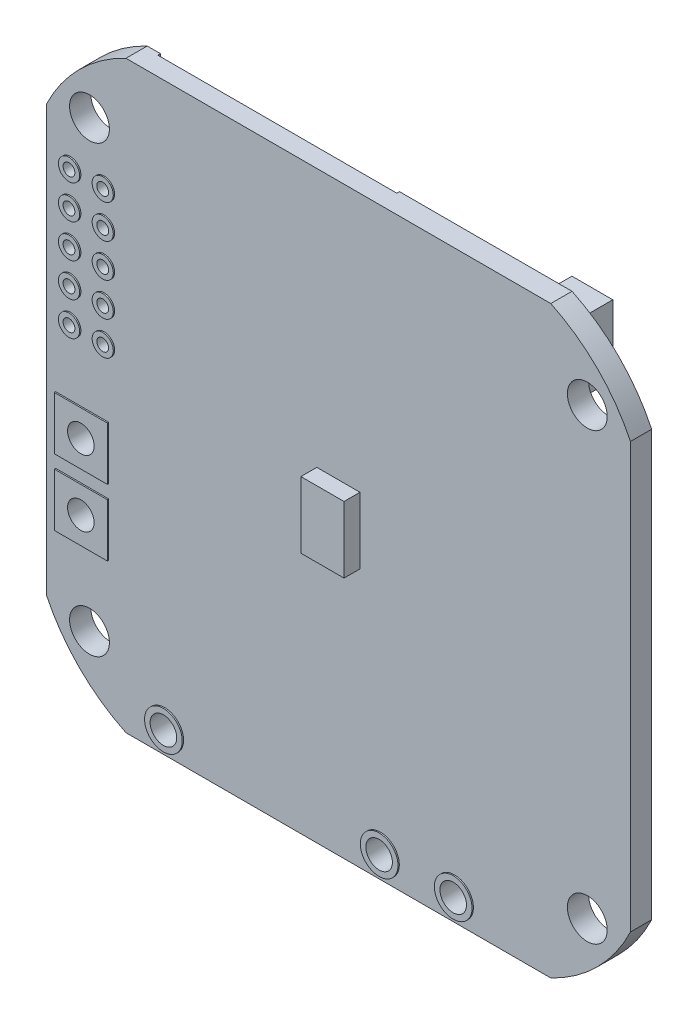
SolidWorks part; units mm, degrees
material "6061-T6 (SS)"
ref_plane "Alzado" through (0, 0, 0) normal (0, 0, 1) x (1, 0, 0)
ref_plane "Planta" through (0, 0, 0) normal (0, 1, 0) x (1, 0, 0)
ref_plane "Vista lateral" through (0, 0, 0) normal (1, 0, 0) x (0, 0, -1)
sketch "Croquis1" plane through (0, 0, 0) normal (0, 0, 1) x (1, 0, 0)
  line L0 (-22, 16) -> (-22, -16)
  line L1 (0, 0) -> (0, -6.2515) construction
  line L2 (22, 16) -> (22, -16)
  line L3 (-16, -22) -> (16, -22)
  line L4 (0, 0) -> (8.2976, 0) construction
  line L5 (-16, 22) -> (16, 22)
  arc A0 (-16, 22) -> (-22, 16) centre (-10.4982, 10.4982) ccw
  arc A2 (16, -22) -> (22, -16) centre (10.4982, -10.4982) ccw
  arc A3 (-22, -16) -> (-16, -22) centre (-10.4982, -10.4982) ccw
  arc A7 (22, 16) -> (16, 22) centre (10.4982, 10.4982) ccw
  point P0 (0, 0)
  point P4 (-22, 0)
  point P13 (0, -22)
  dimension "D3" = 25.5
  dimension "D4" = 32
  dimension "D1" = 32
  dimension "D2" = 22
  dimension "D5" = 22
extrude "Saliente-Extruir1" add sketch "Croquis1" along normal mid plane 1.6
sketch "Croquis2" plane through (0, 0, 0.8) normal (0, 0, 1) x (1, 0, 0)
  line L1 (18.75, -16.75) -> (-18.75, -16.75) construction
  line L2 (18.75, -16.75) -> (18.75, 16.75) construction
  line L3 (18.75, 16.75) -> (-18.75, 16.75) construction
  line L4 (-18.75, -16.75) -> (-18.75, 16.75) construction
  line L5 (18.75, -16.75) -> (-18.75, 16.75) construction
  line L6 (18.75, 16.75) -> (-18.75, -16.75) construction
  circle A0 centre (-18.75, 16.75) radius 1.5
  circle A1 centre (18.75, 16.75) radius 1.5
  circle A2 centre (18.75, -16.75) radius 1.5
  circle A3 centre (-18.75, -16.75) radius 1.5
  point P0 (0, 0)
  dimension "D1" = 3
  dimension "D2" = 37.5
  dimension "D3" = 33.5
extrude "Cortar-Extruir1" cut sketch "Croquis2" against normal through all
sketch "Croquis3" plane through (0, 0, 0.8) normal (0, 0, 1) x (1, 0, 0)
  line L1 (-1.625, 2.5) -> (1.625, 2.5)
  line L2 (-1.625, 2.5) -> (-1.625, -2.5)
  line L3 (-1.625, -2.5) -> (1.625, -2.5)
  line L4 (1.625, 2.5) -> (1.625, -2.5)
  line L5 (-1.625, 2.5) -> (1.625, -2.5) construction
  line L6 (-1.625, -2.5) -> (1.625, 2.5) construction
  point P0 (0, 0)
  dimension "D1" = 5
  dimension "D2" = 3.25
extrude "Saliente-Extruir2" add sketch "Croquis3" along normal blind 1.2
sketch "Croquis4" plane through (0, 0, -0.8) normal (0, 0, -1) x (-1, 0, 0)
  line L0 (22, 16) -> (22, -16) construction
  line L1 (-16, 22) -> (16, 22) construction
  circle A0 centre (17.653, 12.7) radius 0.445
  circle A1 centre (20.193, 12.7) radius 0.445
  circle A2 centre (20.193, 10.16) radius 0.445
  circle A3 centre (20.193, 7.62) radius 0.445
  circle A4 centre (20.193, 5.08) radius 0.445
  circle A5 centre (20.193, 2.54) radius 0.445
  circle A6 centre (17.653, 10.16) radius 0.445
  circle A7 centre (17.653, 7.62) radius 0.445
  circle A8 centre (17.653, 5.08) radius 0.445
  circle A9 centre (17.653, 2.54) radius 0.445
  dimension "D1" = 0.89
  dimension "D3" = 1.807
  dimension "D4" = 9.3
  dimension "D5" = 2.54
  dimension "D2" = 5
extrude "Cortar-Extruir2" cut sketch "Croquis4" against normal through all
sketch "Croquis5" plane through (0, 0, 0) normal (0, 0, 1) x (1, 0, 0)
  line L0 (-16, -22) -> (16, -22) construction
  line L1 (-17.3, -2.4) -> (-21.3, -2.4)
  line L2 (-17.3, -2.4) -> (-17.3, -6.4)
  line L3 (-17.3, -6.4) -> (-21.3, -6.4)
  line L4 (-21.3, -2.4) -> (-21.3, -6.4)
  line L5 (-17.3, -2.4) -> (-21.3, -6.4) construction
  line L6 (-17.3, -6.4) -> (-21.3, -2.4) construction
  line L7 (-17.3, -7.4) -> (-21.3, -7.4)
  line L8 (-17.3, -7.4) -> (-17.3, -11.4)
  line L9 (-17.3, -11.4) -> (-21.3, -11.4)
  line L10 (-21.3, -7.4) -> (-21.3, -11.4)
  line L11 (-17.3, -7.4) -> (-21.3, -11.4) construction
  line L12 (-17.3, -11.4) -> (-21.3, -7.4) construction
  line L13 (-22, 16) -> (-22, -16) construction
  circle A0 centre (-17.653, 2.54) radius 0.7974
  circle A1 centre (-20.193, 2.54) radius 0.7974
  circle A2 centre (-20.193, 5.08) radius 0.7974
  circle A3 centre (-17.653, 5.08) radius 0.7974
  circle A4 centre (-17.653, 7.62) radius 0.7974
  circle A5 centre (-17.653, 10.16) radius 0.7974
  circle A6 centre (-20.193, 7.62) radius 0.7974
  circle A7 centre (-20.193, 10.16) radius 0.7974
  circle A8 centre (-17.653, 12.7) radius 0.7974
  circle A9 centre (-20.193, 12.7) radius 0.7974
  circle A10 centre (-17.653, 12.7) radius 0.445
  circle A11 centre (-20.193, 12.7) radius 0.445
  circle A12 centre (-20.193, 10.16) radius 0.445
  circle A13 centre (-17.653, 10.16) radius 0.445
  circle A14 centre (-17.653, 7.62) radius 0.445
  circle A15 centre (-20.193, 7.62) radius 0.445
  circle A16 centre (-20.193, 5.08) radius 0.445
  circle A17 centre (-17.653, 5.08) radius 0.445
  circle A18 centre (-17.653, 2.54) radius 0.445
  circle A19 centre (-20.193, 2.54) radius 0.445
  point P0 (-19.3, -4.4)
  point P5 (-19.3, -9.4)
  dimension "D1" = 4
  dimension "D2" = 4
  dimension "D3" = 5
  dimension "D4" = 4
  dimension "D5" = 4
  dimension "D6" = 12.6
  dimension "D7" = 2.7
extrude "Saliente-Extruir3" add sketch "Croquis5" along normal mid plane 1.8
sketch "Croquis6" plane through (0, 0, -0.9) normal (0, 0, -1) x (-1, 0, 0)
  line L0 (21.3, -2.4) -> (21.3, -6.4) construction
  line L1 (21.3, -7.4) -> (21.3, -11.4) construction
  circle A0 centre (19.3, -4.4) radius 1
  circle A1 centre (19.3, -9.4) radius 1
  point P6 (21.3, -4.4)
  point P9 (21.3, -9.4)
  dimension "D1" = 2
extrude "Cortar-Extruir3" cut sketch "Croquis6" against normal through all both and the other way through all
sketch "Croquis7" plane through (0, 0, -0.8) normal (0, 0, -1) x (-1, 0, 0)
  line L0 (16, -22) -> (-16, -22) construction
  line L1 (22, 16) -> (22, -16) construction
  circle A0 centre (-8.75, -20.32) radius 1
  circle A1 centre (-3.17, -20.32) radius 1
  circle A2 centre (13.08, -20.32) radius 1
  dimension "D1" = 2
  dimension "D2" = 1.68
  dimension "D3" = 5.58
  dimension "D4" = 16.25
  dimension "D5" = 8.92
extrude "Cortar-Extruir4" cut sketch "Croquis7" against normal blind 10
sketch "Croquis8" plane through (0, 0, -0.8) normal (0, 0, -1) x (-1, 0, 0)
  line L0 (-22, -16) -> (-22, 16) construction
  line L1 (-20.5, 12.95) -> (-17.5, 12.95)
  line L2 (-20.5, 12.95) -> (-20.5, 10.45)
  line L3 (-20.5, 10.45) -> (-17.5, 10.45)
  line L4 (-17.5, 12.95) -> (-17.5, 10.45)
  line L5 (-20.5, 9.95) -> (-17.5, 9.95)
  line L6 (-20.5, 9.95) -> (-20.5, 7.45)
  line L7 (-20.5, 7.45) -> (-17.5, 7.45)
  line L8 (-17.5, 9.95) -> (-17.5, 7.45)
  line L10 (-16, 22) -> (16, 22) construction
  point P8 (-19, 7.45)
  point P11 (-20.5, 11.7)
  point P12 (-20.5, 8.7)
  point P15 (-17.5, 11.7)
  dimension "D1" = 3
  dimension "D2" = 3
  dimension "D3" = 2.5
  dimension "D4" = 3
  dimension "D5" = 10.3
extrude "Saliente-Extruir4" add sketch "Croquis8" along normal blind 1.2
sketch "Croquis9" plane through (0, 0, -2) normal (0, 0, -1) x (-1, 0, 0)
  line L0 (-17.5, 12.95) -> (-20.5, 12.95) construction
  line L1 (-17.5, 7.45) -> (-17.5, 9.95) construction
  line L2 (-17.5, 10.45) -> (-17.5, 12.95) construction
  circle A0 centre (-19, 11.7) radius 0.75
  circle A1 centre (-19, 8.7) radius 0.75
  point P7 (-19, 12.95)
  point P10 (-17.5, 8.7)
  point P14 (-17.5, 11.7)
  dimension "D1" = 1.5
extrude "Saliente-Extruir5" add sketch "Croquis9" along normal blind 0.8
sketch "Croquis10" plane through (0, 0, -0.8) normal (0, 0, -1) x (-1, 0, 0)
  line L0 (-22, -16) -> (-22, 16) construction
  line L1 (-16, -14.25) -> (-11, -14.25)
  line L2 (-16, -14.25) -> (-16, -19.25)
  line L3 (-16, -19.25) -> (-11, -19.25)
  line L4 (-11, -14.25) -> (-11, -19.25)
  line L5 (16, -22) -> (-16, -22) construction
  line L6 (11.25, -12.2) -> (16.25, -12.2)
  line L7 (11.25, -12.2) -> (11.25, -17.2)
  line L8 (11.25, -17.2) -> (16.25, -17.2)
  line L9 (16.25, -12.2) -> (16.25, -17.2)
  line L10 (5.8877, -14.25) -> (10.8877, -14.25)
  line L11 (5.8877, -14.25) -> (5.8877, -19.25)
  line L12 (5.8877, -19.25) -> (10.8877, -19.25)
  line L13 (10.8877, -14.25) -> (10.8877, -19.25)
  line L14 (0.4343, -14.25) -> (5.4343, -14.25)
  line L15 (0.4343, -14.25) -> (0.4343, -19.25)
  line L16 (0.4343, -19.25) -> (5.4343, -19.25)
  line L17 (5.4343, -14.25) -> (5.4343, -19.25)
  line L18 (22, 16) -> (22, -16) construction
  line L19 (-4.9483, -12.2) -> (0.0517, -12.2)
  line L20 (-4.9483, -12.2) -> (-4.9483, -17.2)
  line L21 (-4.9483, -17.2) -> (0.0517, -17.2)
  line L22 (0.0517, -12.2) -> (0.0517, -17.2)
  line L23 (-10.5433, -12.2) -> (-5.5433, -12.2)
  line L24 (-10.5433, -12.2) -> (-10.5433, -17.2)
  line L25 (-10.5433, -17.2) -> (-5.5433, -17.2)
  line L26 (-5.5433, -12.2) -> (-5.5433, -17.2)
  dimension "D1" = 5
  dimension "D2" = 5
  dimension "D3" = 6
  dimension "D4" = 2.75
  dimension "D5" = 5
  dimension "D6" = 5
  dimension "D7" = 5
  dimension "D8" = 5
  dimension "D9" = 5
  dimension "D10" = 5
  dimension "D11" = 5.75
  dimension "D12" = 4.8
  dimension "D13" = 5
  dimension "D14" = 5
  dimension "D15" = 5
  dimension "D16" = 5
extrude "Saliente-Extruir6" add sketch "Croquis10" along normal blind 0.9
sketch "Croquis11" plane through (0, 0, -0.8) normal (0, 0, -1) x (-1, 0, 0)
  line L0 (-13.6529, -19.5225) -> (-10.4593, -19.5225)
  line L1 (-10.4593, -19.5225) -> (-9.8124, -18.8756)
  line L2 (-9.8124, -18.8756) -> (-7.529, -18.8756)
  line L3 (-7.529, -18.8756) -> (-7.1476, -19.257)
  line L4 (-7.1476, -19.257) -> (-7.1476, -21.3437)
  line L5 (-7.1476, -21.3437) -> (-7.529, -21.7251)
  line L6 (-7.529, -21.7251) -> (-13.8301, -21.7251)
  line L7 (-13.8301, -21.7251) -> (-14.1414, -21.4138)
  line L8 (-14.1414, -21.4138) -> (-14.1414, -20.011)
  line L9 (-14.1414, -20.011) -> (-13.6529, -19.5225)
  line L10 (8.1723, -19.5225) -> (11.1983, -19.5225)
  line L11 (11.1983, -19.5225) -> (12.0225, -18.6983)
  line L12 (12.0225, -18.6983) -> (14.2962, -18.6983)
  line L13 (14.2962, -18.6983) -> (14.7785, -19.1806)
  line L14 (14.7785, -19.1806) -> (14.7785, -21.2429)
  line L15 (14.7785, -21.2429) -> (14.2962, -21.7251)
  line L16 (14.2962, -21.7251) -> (7.9951, -21.7251)
  line L17 (7.9951, -21.7251) -> (7.6839, -21.4138)
  line L18 (7.6839, -21.4138) -> (7.6839, -20.011)
  line L19 (7.6839, -20.011) -> (8.1723, -19.5225)
  line L20 (2.2631, -20.011) -> (1.7746, -19.5225)
  line L21 (2.2631, -21.4138) -> (2.2631, -20.011)
  line L22 (1.9518, -21.7251) -> (2.2631, -21.4138)
  line L23 (-4.3493, -21.7251) -> (1.9518, -21.7251)
  line L24 (-4.7307, -21.3437) -> (-4.3493, -21.7251)
  line L25 (-4.7307, -19.257) -> (-4.7307, -21.3437)
  line L26 (-4.3493, -18.8756) -> (-4.7307, -19.257)
  line L27 (-2.0659, -18.8756) -> (-4.3493, -18.8756)
  line L28 (-1.4189, -19.5225) -> (-2.0659, -18.8756)
  line L29 (1.7746, -19.5225) -> (-1.4189, -19.5225)
  line L30 (-5.9391, -18.0693) -> (-5.9391, -23.1735) construction
  circle A0 centre (-8.75, -20.32) radius 1
  circle A1 centre (-3.17, -20.32) radius 1
  circle A2 centre (13.08, -20.32) radius 1
extrude "Saliente-Extruir7" add sketch "Croquis11" along normal blind 0.1
sketch "Croquis12" plane through (0, 0, -0.8) normal (0, 0, -1) x (-1, 0, 0)
  line L0 (-19.5752, -2.7898) -> (-13.4845, -8.8805)
  line L1 (-19.5752, -2.7898) -> (-13.4845, 3.301)
  line L2 (-13.4845, -8.8805) -> (-7.3937, -2.7898)
  line L3 (-13.4845, 3.301) -> (-7.3937, -2.7898)
  line L4 (16, -22) -> (-16, -22) construction
  dimension "D1" = 45
extrude "Saliente-Extruir8" add sketch "Croquis12" along normal blind 0.75
sketch "Croquis13" plane through (0, 0, -0.8) normal (0, 0, -1) x (-1, 0, 0)
  line L1 (-16.4217, 20.3319) -> (-13.3413, 20.3319)
  line L2 (-16.4217, 20.3319) -> (-16.4217, 15.0982)
  line L3 (-16.4217, 15.0982) -> (-13.3413, 15.0982)
  line L4 (-13.3413, 20.3319) -> (-13.3413, 15.0982)
extrude "Saliente-Extruir9" add sketch "Croquis13" along normal blind 2.65
sketch "Croquis14" plane through (0, 0, -0.8) normal (0, 0, -1) x (-1, 0, 0)
  line L1 (-12.0511, 17.4084) -> (-8.2311, 17.4084)
  line L2 (-12.0511, 17.4084) -> (-12.0511, 13.5884)
  line L3 (-12.0511, 13.5884) -> (-8.2311, 13.5884)
  line L4 (-8.2311, 17.4084) -> (-8.2311, 13.5884)
  dimension "D1" = 3.82
extrude "Saliente-Extruir10" add sketch "Croquis14" along normal blind 3
sketch "Croquis30" plane through (0, 0, 0.8) normal (0, 0, 1) x (1, 0, 0)
  circle A0 centre (-13.08, -20.32) radius 1.4199
  circle A1 centre (8.75, -20.32) radius 1.4199
  circle A2 centre (3.17, -20.32) radius 1.4199
  circle A3 centre (-13.08, -20.32) radius 1
  circle A4 centre (3.17, -20.32) radius 1
  circle A5 centre (8.75, -20.32) radius 1
extrude "Saliente-Extruir17" add sketch "Croquis30" along normal blind 0.1
sketch "Croquis29" plane through (0, 0, -0.8) normal (0, 0, -1) x (-1, 0, 0)
  line L0 (-16, 22) -> (16, 22) construction
  line L1 (10.5, 1.5) -> (14, 1.5)
  line L2 (10.5, 1.5) -> (10.5, 0)
  line L3 (10.5, 0) -> (14, 0)
  line L4 (14, 1.5) -> (14, 0)
  line L5 (10.5, -0.65) -> (14, -0.65)
  line L6 (10.5, -0.65) -> (10.5, -2.15)
  line L7 (10.5, -2.15) -> (14, -2.15)
  line L8 (14, -0.65) -> (14, -2.15)
  line L9 (2.75, 1.5) -> (6.25, 1.5)
  line L10 (2.75, 1.5) -> (2.75, 0)
  line L11 (2.75, 0) -> (6.25, 0)
  line L12 (6.25, 1.5) -> (6.25, 0)
  line L13 (22, 16) -> (22, -16) construction
  dimension "D1" = 3.5
  dimension "D2" = 1.5
  dimension "D3" = 0.65
  dimension "D4" = 3.5
  dimension "D5" = 20.5
  dimension "D6" = 11.5
  dimension "D7" = 7.75
extrude "Saliente-Extruir16" add sketch "Croquis29" along normal blind 0.5
chamfer "Chaflán1" distance 1 angle 45 4 edges at (12.0511, 17.4084, -2.3) (8.2311, 17.4084, -2.3) (12.0511, 13.5884, -2.3) (8.2311, 13.5884, -2.3)
sketch "Croquis31" plane through (0, 0, -0.8) normal (0, 0, -1) x (-1, 0, 0)
  line L0 (-16, 22) -> (16, 22) construction
  line L1 (-3, 22) -> (15, 22)
  line L2 (-3, 22) -> (-3, 2.65)
  line L3 (-3, 2.65) -> (15, 2.65)
  line L4 (15, 22) -> (15, 2.65)
  line L5 (22, 16) -> (22, -16) construction
  dimension "D1" = 19.35
  dimension "D2" = 18
  dimension "D3" = 7
extrude "Cortar-Extruir5" cut sketch "Croquis31" against normal blind 0.2
